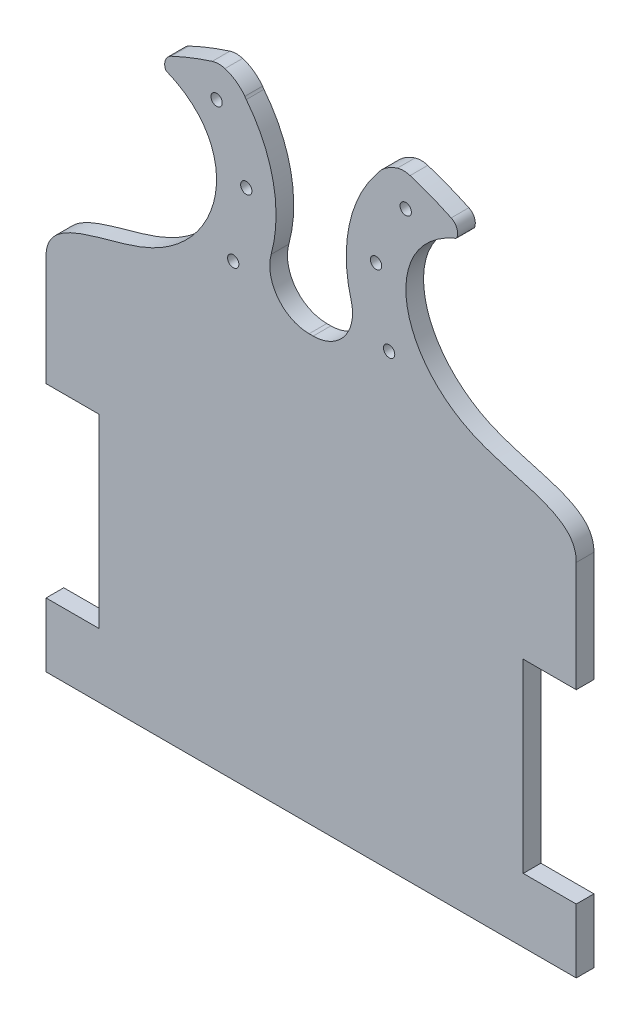
SolidWorks part; units mm, degrees
ref_plane "Front Plane" through (0, 0, 0) normal (0, 0, 1) x (1, 0, 0)
ref_plane "Top Plane" through (0, 0, 0) normal (0, 1, 0) x (1, 0, 0)
ref_plane "Right Plane" through (0, 0, 0) normal (1, 0, 0) x (0, 0, -1)
sketch "Sketch1" plane through (0, 0, 0) normal (0, 0, 1) x (1, 0, 0)
  line L0 (0, 75) -> (0, -90.625) construction
  line L1 (-75, -90.625) -> (75, -90.625)
  line L2 (-75, -90.625) -> (-75, 11.4006)
  line L4 (75, -90.625) -> (75, 11.1914)
  line L5 (-75, -90.625) -> (25.8496, 31.235) construction
  line L6 (-24.3745, 29.4525) -> (75, -90.625) construction
  line L7 (75, -72.5) -> (60, -72.5)
  line L8 (-75, -20) -> (-60, -20)
  line L9 (-75, -20) -> (-75, -72.5)
  line L10 (-75, -72.5) -> (-60, -72.5)
  line L11 (-60, -20) -> (-60, -72.5)
  line L12 (60, -20) -> (60, -72.5)
  line L13 (75, -20) -> (60, -20)
  line L14 (75, -20) -> (75, -72.5)
  line L15 (-0.5732, 29.4525) -> (0.5732, 29.4525)
  line L17 (-0.5732, 29.4525) -> (0.5732, 29.4525)
  arc A0 (40.9813, 73.6285) -> (40.7979, 73.5292) centre (39.7504, 75.683) cw
  arc A2 (39.6203, 77.9294) -> (27.9943, 82.4888) centre (-0.7855, -8) ccw
  arc A5 (-11.3131, 43.5336) -> (-18.3641, 77.9294) centre (-48.71, 53.788) ccw
  arc A6 (11.3131, 43.5336) -> (18.3641, 77.9294) centre (48.71, 53.788) cw
  arc A7 (-18.7714, 78.527) -> (-18.3641, 77.9294) centre (-14.519, 80.9883) ccw
  arc A8 (-39.6203, 77.9294) -> (-27.9943, 82.4888) centre (0.7855, -8) cw
  arc A9 (27.9943, 82.4888) -> (24.389, 82.5123) centre (26.1538, 76.7019) ccw
  arc A10 (-0.5732, 29.4525) -> (-11.3131, 43.5336) centre (-0.5732, 40.5887) cw
  arc A11 (0.5732, 29.4525) -> (11.3131, 43.5336) centre (0.5732, 40.5887) ccw
  circle A12 centre (-18.3641, 56.2921) radius 1.6
  circle A13 centre (-26.7535, 73.6912) radius 1.6
  circle A14 centre (-22.0529, 36.4833) radius 1.6
  circle A15 centre (22.0529, 36.4833) radius 1.6
  circle A16 centre (26.7535, 73.6912) radius 1.6
  circle A17 centre (18.3641, 56.2921) radius 1.6
  arc A18 (18.3641, 77.9294) -> (24.389, 82.5123) centre (27.5501, 72.1047) cw
  arc A19 (-41.2107, 73.8624) -> (-39.6203, 77.9294) centre (-38.2589, 75.0526) cw
  arc A21 (-41.2107, 73.8624) -> (-40.9813, 73.6285) centre (-40.7979, 74.0379) ccw
  arc A22 (41.2107, 73.8624) -> (39.6203, 77.9294) centre (38.2589, 75.0526) ccw
  arc A23 (41.2107, 73.8624) -> (40.9813, 73.6285) centre (40.7979, 74.0379) cw
  arc A24 (-27.9943, 82.4888) -> (-24.389, 82.5123) centre (-26.1538, 76.7019) cw
  arc A25 (-18.3641, 77.9294) -> (-24.389, 82.5123) centre (-27.5501, 72.1047) ccw
  arc A26 (-18.3641, 77.9294) -> (-24.389, 82.5123) centre (-27.5501, 72.1047) ccw
  spline S0 degree 3 poles (-40.9813, 73.6285) (-29.0364, 68.7458) (-21.6827, 49.9534) (-43.852, 22.5324) (-75.1065, 22.3554) (-75, 11.1914) knots 0.184913 0.184913 0.184913 0.184913 0.468621 0.712803 1 1 1 1
  spline S1 degree 3 poles (40.7979, 73.5292) (29.1134, 68.5841) (21.6988, 49.8372) (43.8722, 22.5383) (75.1065, 22.3554) (75, 11.1914) knots 0.187825 0.187825 0.187825 0.187825 0.468621 0.712803 1 1 1 1
  point P0 (0, 0)
  point P31 (-0.7855, 96.9552)
  point P49 (26.5495, 82.9357)
  dimension "D1" = 15
  dimension "D3" = 4.9134
  dimension "D4" = 11.1362
  dimension "D5" = 3.2
  dimension "D7" = 6.0725
  dimension "D2" = 52.5
extrude "Boss-Extrude1" add sketch "Sketch1" along normal blind 5 contours S1 A0 A23 A22 A2 A9 A18 A6 A11 L15 A10 A5 A7 A25 A24 A8 A19 A21 S0 L2 L8 L11 L10 L1 L4 L7 L12 L13 A16 A12 A13 A14 A15 A17
